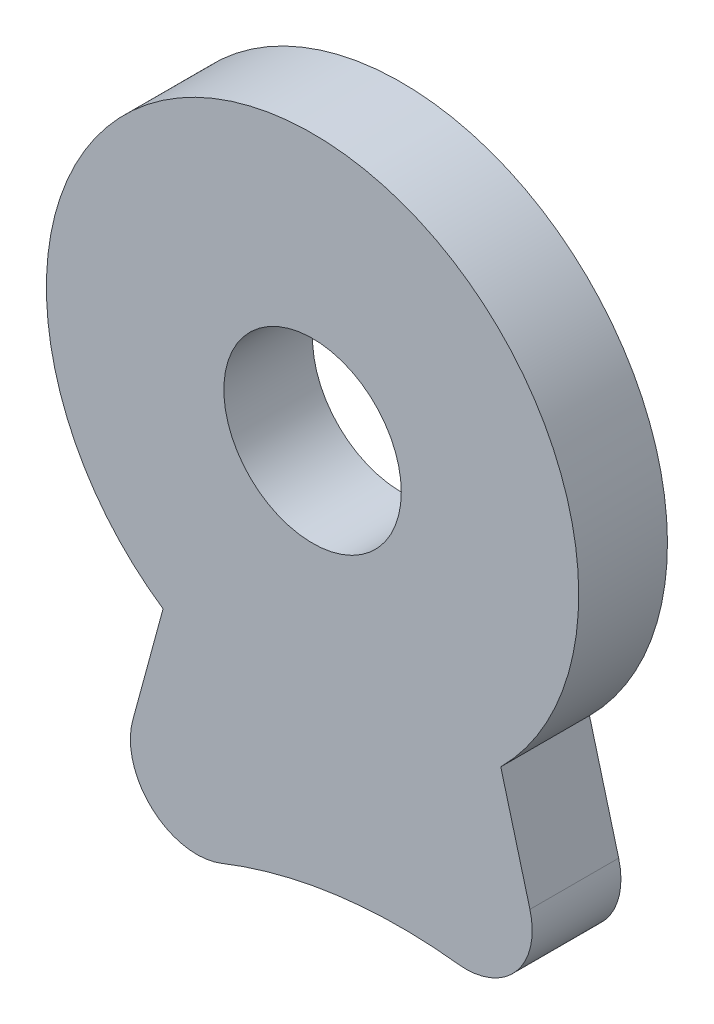
SolidWorks part; units mm, degrees
ref_plane "Front Plane" through (0, 0, 0) normal (0, 0, 1) x (1, 0, 0)
ref_plane "Top Plane" through (0, 0, 0) normal (0, 1, 0) x (1, 0, 0)
ref_plane "Right Plane" through (0, 0, 0) normal (1, 0, 0) x (0, 0, -1)
sketch "Sketch1" plane through (0, 0, 0) normal (0, 0, 1) x (1, 0, 0)
  line L0 (-177.7863, -30.1363) -> (-179.4321, -36.2)
  line L1 (-170.1736, -29.4148) -> (-168.876, -34.2574)
  circle A0 centre (-174.4163, -25.1722) radius 6
  arc A1 (-179.4321, -36.2) -> (-168.876, -34.2574) centre (-172.4163, -44.6722) cw
  circle A4 centre (-174.4163, -25.1722) radius 2
  point P8 (-174.4163, -25.1722)
  dimension "D2" = 12
  dimension "D1" = 4
  dimension "D3" = 11
  dimension "D4" = 168.876
  dimension "D5" = 170.1736
  dimension "D6" = 172.4163
  dimension "D7" = 177.7863
  dimension "D8" = 179.4321
  dimension "D9" = 34.2574
extrude "Boss-Extrude1" add sketch "Sketch1" along normal blind 2 contours A0 A4 | L0 A1 L1 A0
fillet "Fillet1" radius 1.5 2 edges at (-179.4321, -36.2, 1) (-168.876, -34.2574, 1)
